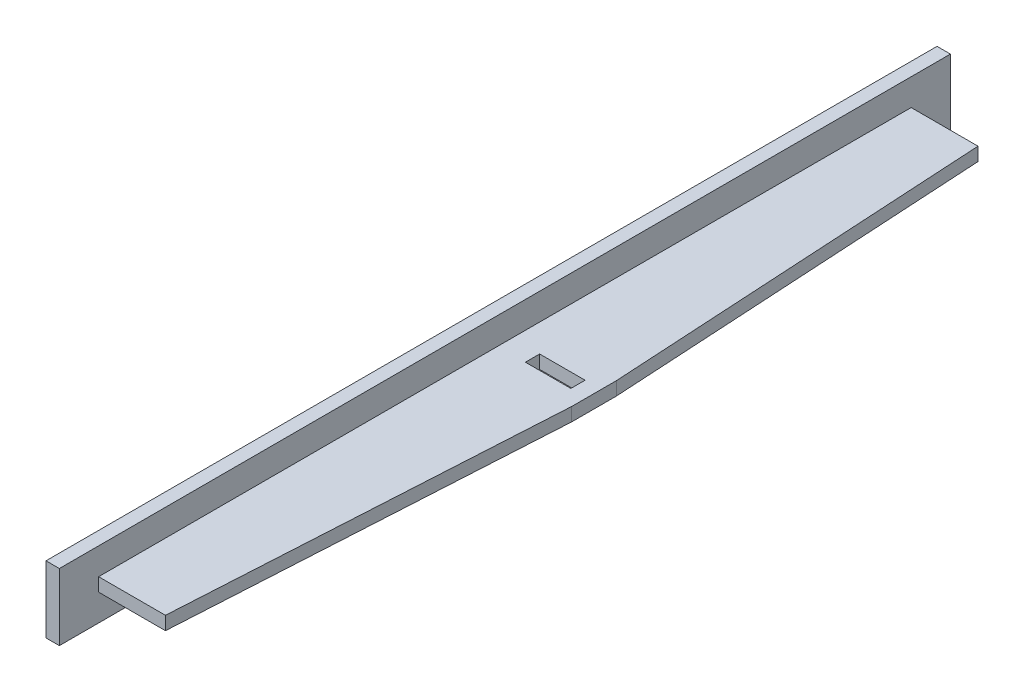
SolidWorks part; units mm, degrees
ref_plane "前视基准面" through (0, 0, 0) normal (0, 0, 1) x (1, 0, 0)
ref_plane "上视基准面" through (0, 0, 0) normal (0, 1, 0) x (1, 0, 0)
ref_plane "右视基准面" through (0, 0, 0) normal (1, 0, 0) x (0, 0, -1)
other "Configuration Table"
sketch "草图1" plane through (0, 0, 0) normal (0, 0, 1) x (1, 0, 0)
  line L1 (0, 0) -> (3, 0)
  line L2 (0, 0) -> (0, 15)
  line L3 (0, 15) -> (3, 15)
  line L4 (3, 0) -> (3, 15)
  dimension "D1" = 15
  dimension "D2" = 3
extrude "凸台-拉伸1" add sketch "草图1" along normal blind 200
ref_plane "基准面1" through (0, 9, 0) normal (0, 1, 0) x (1, 0, 0)
sketch "草图12" plane through (0, 9, 0) normal (0, 1, 0) x (1, 0, 0)
  line L0 (3, -100) -> (91.3211, -100) construction
  line L1 (18, -191.19) -> (23, -105)
  line L2 (3, -8.81) -> (18, -8.81)
  line L3 (3, -200) -> (3, 0) construction
  line L4 (18, -8.81) -> (23, -95)
  line L5 (23, -95) -> (23, -105)
  line L6 (3, -8.81) -> (3, -191.19)
  line L7 (3, -191.19) -> (18, -191.19)
  point P6 (23, -95)
  point P12 (3, -100)
  point P13 (23, -100)
  dimension "D1" = 5
  dimension "D2" = 20
  dimension "D3" = 15
  dimension "D4" = 8.81
extrude "凸台-拉伸7" add sketch "草图12" against normal blind 3
sketch "草图13" plane through (0, 6, 0) normal (0, -1, 0) x (1, 0, 0)
  line L0 (23, 105) -> (23, 95) construction
  line L1 (9.2, 101.6) -> (19.4, 101.6)
  line L2 (9.2, 101.6) -> (9.2, 98.4)
  line L3 (9.2, 98.4) -> (19.4, 98.4)
  line L4 (19.4, 101.6) -> (19.4, 98.4)
  line L5 (9.2, 101.6) -> (19.4, 98.4) construction
  line L6 (9.2, 98.4) -> (19.4, 101.6) construction
  point P0 (14.3, 100)
  dimension "D1" = 8.7
  dimension "D2" = 10.2
  dimension "D3" = 3.2
  dimension "D4" = 5
extrude "切除-拉伸2" cut sketch "草图13" against normal blind 23
